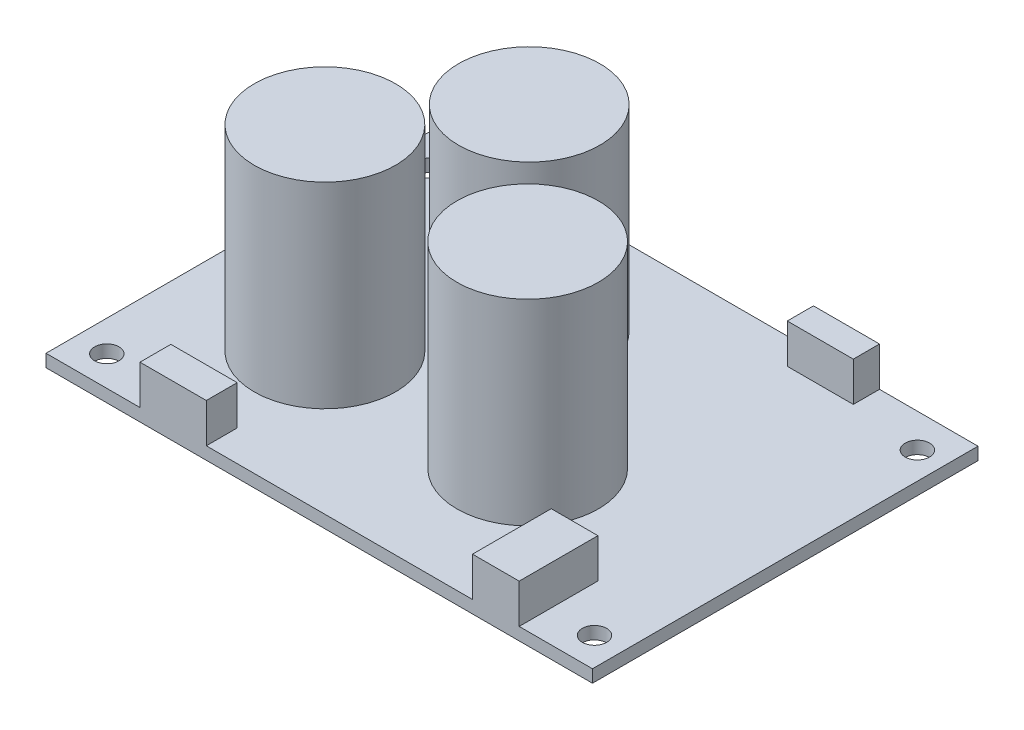
SolidWorks part; units mm, degrees
ref_plane "Front" through (0, 0, 0) normal (0, 0, 1) x (1, 0, 0)
ref_plane "Top" through (0, 0, 0) normal (0, 1, 0) x (1, 0, 0)
ref_plane "Right" through (0, 0, 0) normal (1, 0, 0) x (0, 0, -1)
sketch "Sketch1" plane through (0, 0, 0) normal (0, 1, 0) x (1, 0, 0)
  line L1 (0, 0) -> (69.6, 0)
  line L2 (0, 0) -> (0, -49.1)
  line L3 (0, -49.1) -> (69.6, -49.1)
  line L4 (69.6, 0) -> (69.6, -49.1)
  dimension "D1" = 69.6
  dimension "D2" = 49.1
extrude "Boss-Extrude1" add sketch "Sketch1" along normal blind 1.6
sketch "Sketch2" plane through (0, 1.6, 0) normal (0, 1, 0) x (1, 0, 0)
  circle A0 centre (17.5288, -31.1082) radius 9
  circle A1 centre (28.3278, -15.8843) radius 9
  circle A2 centre (43.3529, -31.1082) radius 9
  dimension "D1" = 18
  dimension "D2" = 18
  dimension "D3" = 18
extrude "Boss-Extrude2" add sketch "Sketch2" along normal blind 25
sketch "Sketch3" plane through (0, 1.6, 0) normal (0, 1, 0) x (1, 0, 0)
  line L0 (0, 0) -> (0, -49.1) construction
  line L1 (69.6, 0) -> (0, 0) construction
  line L2 (69.6, -49.1) -> (69.6, 0) construction
  line L4 (0, -49.1) -> (69.6, -49.1) construction
  circle A0 centre (3.937, -4.318) radius 1.55
  circle A1 centre (66.17, -4.29) radius 1.55
  circle A2 centre (66.044, -45.29) radius 1.55
  circle A3 centre (3.937, -45.29) radius 1.55
  point P12 (0, 0)
  point P15 (0, 0)
  dimension "D1" = 3.1
  dimension "D2" = 3.1
  dimension "D3" = 3.1
  dimension "D4" = 3.1
  dimension "D5" = 3.937
  dimension "D6" = 4.318
  dimension "D7" = 4.29
  dimension "D8" = 3.43
  dimension "D9" = 3.937
  dimension "D10" = 3.81
  dimension "D11" = 3.556
  dimension "D12" = 3.81
extrude "Cut-Extrude1" cut sketch "Sketch3" against normal through all
sketch "Sketch4" plane through (0, 1.6, 0) normal (0, 1, 0) x (1, 0, 0)
  line L0 (69.6, 0) -> (0, 0) construction
  line L1 (13.7786, 0) -> (20.9138, 0)
  line L2 (13.7786, 0) -> (13.7786, -3.6348)
  line L3 (13.7786, -3.6348) -> (20.9138, -3.6348)
  line L4 (20.9138, 0) -> (20.9138, -3.6348)
  line L5 (0, -49.1) -> (69.6, -49.1) construction
  line L6 (48.6444, 0) -> (57.0562, 0)
  line L7 (48.6444, 0) -> (48.6444, -3.336)
  line L8 (48.6444, -3.336) -> (57.0562, -3.336)
  line L9 (57.0562, 0) -> (57.0562, -3.336)
  line L10 (11.968, -49.1) -> (20.4169, -49.1)
  line L11 (11.968, -49.1) -> (11.968, -45.1661)
  line L12 (11.968, -45.1661) -> (20.4169, -45.1661)
  line L13 (20.4169, -49.1) -> (20.4169, -45.1661)
  line L15 (54.3194, -49.1) -> (60.2646, -49.1)
  line L16 (54.3194, -49.1) -> (54.3194, -39.0733)
  line L17 (54.3194, -39.0733) -> (60.2646, -39.0733)
  line L18 (60.2646, -49.1) -> (60.2646, -39.0733)
extrude "Boss-Extrude3" add sketch "Sketch4" along normal blind 5
